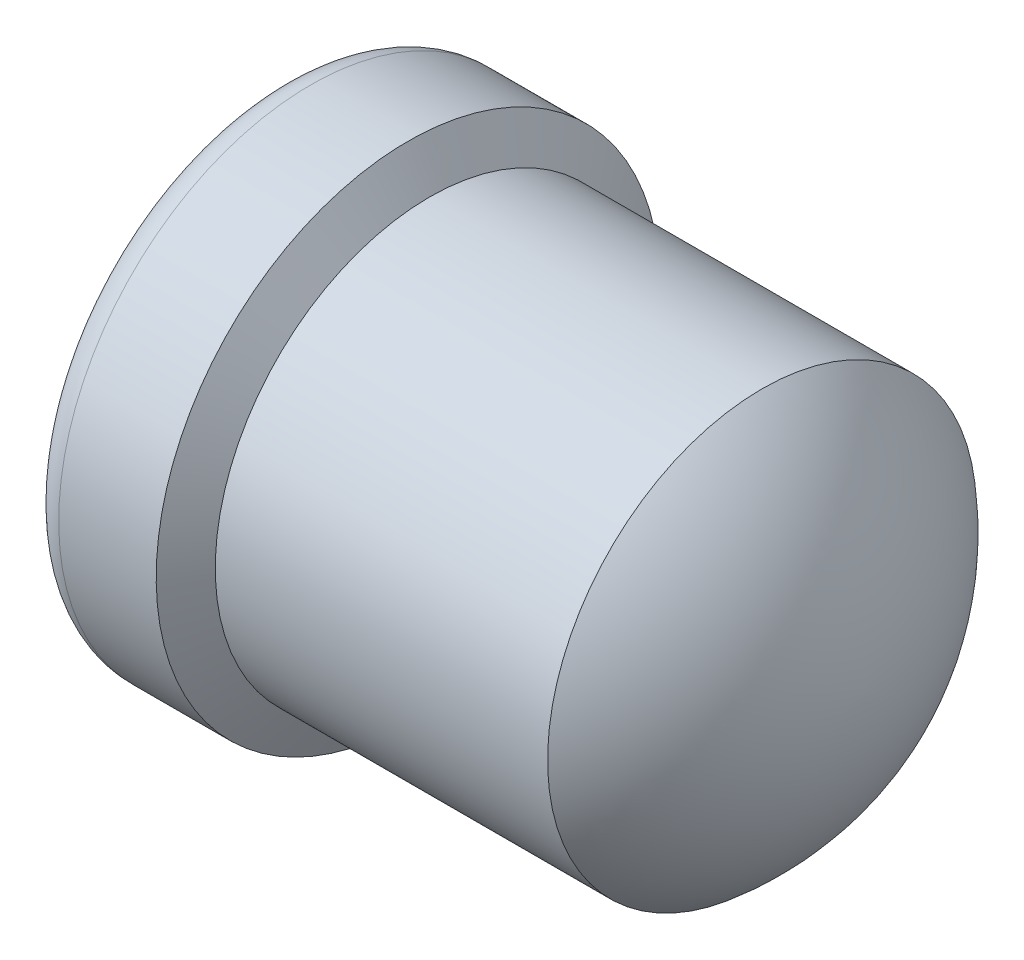
SolidWorks part; units mm, degrees
material "Brass Alloy 385"
ref_plane "Front Plane" through (0, 0, 0) normal (0, 0, 1) x (1, 0, 0)
ref_plane "Top Plane" through (0, 0, 0) normal (0, 1, 0) x (1, 0, 0)
ref_plane "Right Plane" through (0, 0, 0) normal (1, 0, 0) x (0, 0, -1)
sketch "Sketch1" plane through (0, 0, 0) normal (0, 0, 1) x (1, 0, 0)
  line L0 (0, 0) -> (0, 0.5474)
  line L1 (0.0762, 0.6236) -> (0.3175, 0.6236)
  line L2 (0.3175, 0.6236) -> (0.371, 0.5309)
  line L3 (1.1938, 0.5309) -> (0.371, 0.5309)
  line L5 (0, 0) -> (1.4478, 0)
  line L6 (0, 0) -> (1.4478, 0) construction
  arc A0 (1.4478, 0) -> (1.1938, 0.5309) centre (0.7367, -0.014) ccw
  arc A1 (0.0762, 0.6236) -> (0, 0.5474) centre (0.0762, 0.5474) ccw
  point P11 (0, 0.6236)
revolve "RevolutionAngle1" add sketch "Sketch1" angle 360 about L6
hole_wizard "Hole1" positions "Sketch3" profile "Sketch2" legacy
sketch "Sketch3" plane through (0, 0, 0) normal (-1, 0, 0) x (0, 0, 1)
  point P0 (0, 0)
sketch "Sketch2" plane through (0, 0, 0) normal (0, 1, 0) x (0, 0, 1)
  line L0 (0, 0) -> (0, 1.2907)
  line L1 (0, 1.2907) -> (0.4572, 1.016)
  line L2 (0.4572, 1.016) -> (0.4572, 0.154)
  line L3 (0.4572, 0.154) -> (0.5461, 0)
  line L4 (0.5461, 0) -> (0, 0)
  line L5 (0, -14.3089) -> (0, 102.4216) construction
  line L6 (0, 1.2907) -> (-0.4572, 1.016) construction
  line L7 (-0.4572, 0.154) -> (-0.5461, 0) construction
  dimension "A" = 0.9144
  dimension "N" = 1.016
  dimension "B" = 1.0922
  dimension "P1" = 60
  dimension "Drill Angle" = 118
